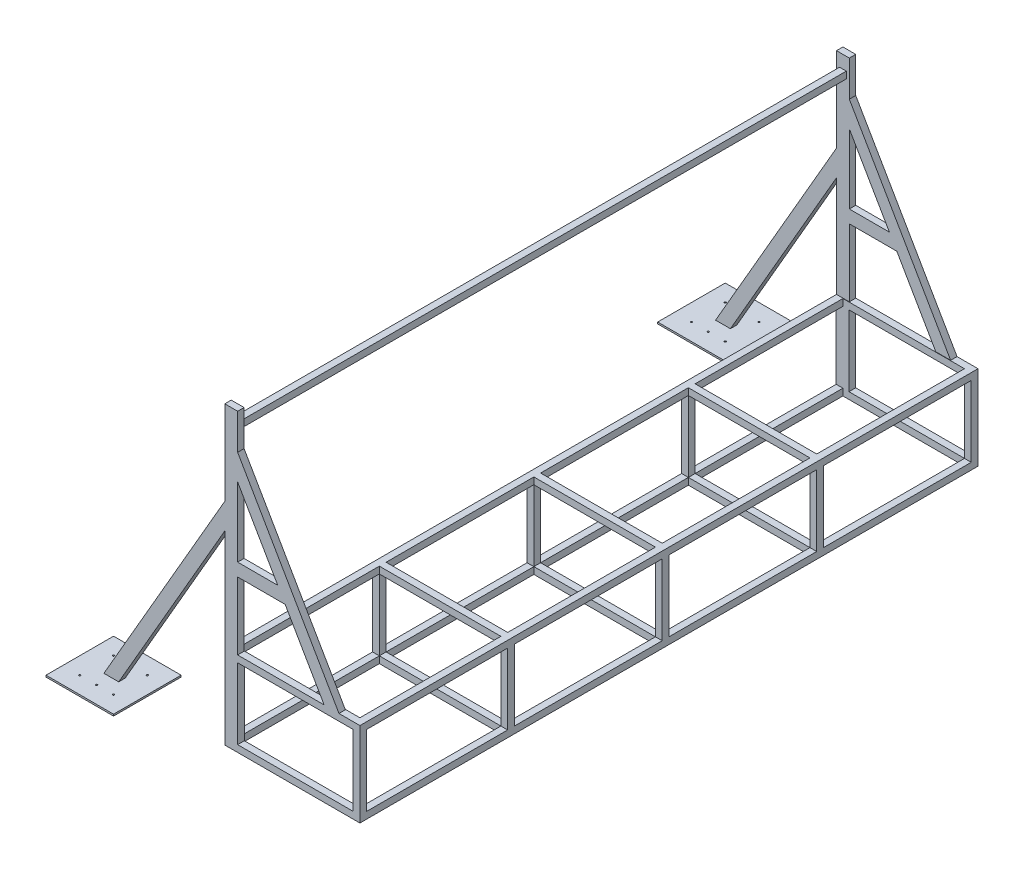
SolidWorks part; units mm, degrees
ref_plane "Front Plane" through (0, 0, 0) normal (0, 0, 1) x (1, 0, 0)
ref_plane "Top Plane" through (0, 0, 0) normal (0, 1, 0) x (1, 0, 0)
ref_plane "Right Plane" through (0, 0, 0) normal (1, 0, 0) x (0, 0, -1)
sketch "Sketch1" plane through (0, 0, 0) normal (0, 0, 1) x (1, 0, 0)
  line L0 (0, 0) -> (800, 0)
  line L1 (55, 0) -> (-55, 0) construction
  line L4 (800, 500) -> (800, 1426.2248) construction
  line L6 (0, 0) -> (0, 500)
  line L7 (0, 500) -> (800, 500)
  line L8 (800, 500) -> (800, 0)
  line L9 (0, 500) -> (0, 2000)
  line L10 (800, 500) -> (2630, 3669.653)
  line L11 (1715, 2084.8265) -> (0, 2000) construction
  line L12 (800, 0) -> (5182.5126, 0) construction
  line L13 (2805.4283, 4100) -> (3005.4283, 4100)
  line L14 (5.4283, 4100) -> (205.4283, 4100)
  line L15 (5.4283, 4100) -> (5.4283, 3700)
  line L16 (5.4283, 3700) -> (205.4283, 3700)
  line L17 (205.4283, 4100) -> (205.4283, 3700)
  line L18 (5.4283, 4100) -> (205.4283, 3700) construction
  line L19 (5.4283, 3700) -> (205.4283, 4100) construction
  line L20 (2805.4283, 4100) -> (2805.4283, 3700)
  line L21 (2805.4283, 3700) -> (3005.4283, 3700)
  line L22 (3005.4283, 4100) -> (3005.4283, 3700)
  line L23 (2805.4283, 4100) -> (3005.4283, 3700) construction
  line L24 (2805.4283, 3700) -> (3005.4283, 4100) construction
  line L25 (800, 500) -> (784.4115, 509)
  line L26 (1715, 2084.8265) -> (1160.2235, 2405.1269) construction
  line L27 (2630, 3669.653) -> (2630, 2940.232) construction
  line L28 (2630, 3669.653) -> (3156.2133, 3365.8436) construction
  line L29 (784.4115, 509) -> (2614.4115, 3678.653)
  line L30 (2614.4115, 3678.653) -> (2630, 3669.653)
  line L31 (5605.4283, 4100) -> (5805.4283, 4100)
  line L32 (5605.4283, 4100) -> (5605.4283, 3700)
  line L33 (5605.4283, 3700) -> (5805.4283, 3700)
  line L34 (5805.4283, 4100) -> (5805.4283, 3700)
  line L35 (5605.4283, 4100) -> (5805.4283, 3700) construction
  line L36 (5605.4283, 3700) -> (5805.4283, 4100) construction
  point P5 (105.4283, 3900)
  point P17 (2905.4283, 3900)
  point P22 (5705.4283, 3900)
  dimension "D1" = 800
  dimension "D2" = 500
  dimension "D3" = 1500
  dimension "D4" = 3660
  dimension "D5" = 30
  dimension "D6" = 3669.653
  dimension "D7" = 2630
  dimension "D8" = 1717.0965
  dimension "D9" = 200
  dimension "D10" = 400
  dimension "D11" = 3700
  dimension "D12" = 200
  dimension "D13" = 400
  dimension "D17" = 90
  dimension "D18" = 32.832
  dimension "D19" = 90
  dimension "D14" = 2600
  dimension "D15" = 18
  dimension "D16" = 200
  dimension "D20" = 400
  dimension "D21" = 2600
extrude "Boss-Extrude5" add sketch "Sketch1" along normal blind 3660 contours L8 L7 L6 L0 | L30 L29 L25 L10
ref_plane "Plane1" through (0, 0, 1830) normal (0, 0, 1) x (1, 0, 0)
sketch "Sketch3" plane through (0, 0, 0) normal (0, 0, 1) x (1, 0, 0)
  line L0 (0, 0) -> (-1677.1081, 0) construction
  line L1 (0, 500) -> (76, 500)
  line L2 (0, 500) -> (0, 1098)
  line L3 (0, 1750) -> (76, 1750)
  line L4 (76, 500) -> (76, 900)
  line L5 (0, 1250) -> (-721.6878, 0)
  line L6 (0, 1098) -> (-633.9306, 0)
  line L7 (0, 1250) -> (0, 1750)
  line L8 (0, 500) -> (0, 2000) construction
  line L9 (-633.9306, 0) -> (-721.6878, 0)
  line L10 (76, 1539.2305) -> (676, 500)
  line L11 (0, 500) -> (800, 500) construction
  line L12 (76, 1387.2305) -> (313.424, 976)
  line L14 (676, 500) -> (588.2428, 500)
  line L15 (76, 1539.2305) -> (76, 1750)
  line L16 (76, 976) -> (313.424, 976)
  line L17 (76, 900) -> (357.3027, 900)
  line L18 (76, 976) -> (76, 1387.2305)
  line L19 (357.3027, 900) -> (588.2428, 500)
  point P21 (376, 1019.6152)
  point P22 (-677.8092, 0)
  dimension "D3" = 76
  dimension "D4" = 1200
  dimension "D6" = 60
  dimension "D1" = 76
  dimension "D5" = 76
  dimension "D7" = 60
  dimension "D2" = 1750
  dimension "D8" = 76
  dimension "D9" = 400
extrude "Boss-Extrude2" add sketch "Sketch3" along normal blind 38
mirror "Mirror1" about plane through (0, 0, 1830) normal (0, 0, 1) of "Boss-Extrude2"
sketch "Sketch4" plane through (0, 0, 3660) normal (0, 0, 1) x (1, 0, 0)
  line L0 (800, 500) -> (800, 0) construction
  line L1 (76, 460) -> (760, 460)
  line L2 (76, 460) -> (76, 40)
  line L3 (76, 40) -> (760, 40)
  line L4 (760, 460) -> (760, 40)
  line L5 (0, 0) -> (800, 0) construction
  line L7 (0, 500) -> (800, 500) construction
  line L8 (0, 0) -> (0, 1098) construction
  dimension "D3" = 76
  dimension "D1" = 40
  dimension "D2" = 40
  dimension "D4" = 40
extrude "Cut-Extrude1" cut sketch "Sketch4" against normal through all
sketch "Sketch5" plane through (0, 0, 1830) normal (0, 0, 1) x (1, 0, 0)
  line L0 (40, 500) -> (40, 460)
  line L1 (40, 460) -> (0, 460)
  line L2 (0, 460) -> (0, 40)
  line L3 (0, 40) -> (40, 40)
  line L4 (40, 40) -> (40, 0)
  line L5 (40, 0) -> (760, 0)
  line L6 (760, 0) -> (760, 40)
  line L7 (760, 40) -> (800, 40)
  line L8 (800, 40) -> (800, 460)
  line L9 (800, 460) -> (760, 460)
  line L10 (760, 460) -> (760, 500)
  line L11 (760, 500) -> (40, 500)
  line L12 (800, 500) -> (800, 0) construction
  line L13 (0, 500) -> (800, 500) construction
  line L14 (0, 0) -> (0, 500) construction
  line L15 (0, 0) -> (800, 0) construction
  line L17 (0, 0) -> (0, 1098) construction
  dimension "D1" = 40
extrude "Cut-Extrude2" cut sketch "Sketch5" against normal offset from surface 40 and the other way offset from surface (1790 mm away) 40 up to face at (418, 250, 0)
sketch "Sketch7" plane through (367.9052, -212.4102, 0) normal (-0.866, 0.5, 0) x (0, 0, 1)
  line L0 (1830, 833.0127) -> (0, 833.0127)
  line L2 (0, 833.0127) -> (0, 4493.0127)
  line L3 (0, 4493.0127) -> (1830, 4493.0127)
  line L5 (1830, 4493.0127) -> (1830, 4455.0127)
  line L6 (1830, -275) -> (1830, 275) construction
  line L7 (1830, 4455.0127) -> (38, 4455.0127)
  line L8 (38, 4455.0127) -> (38, 871.0127)
  line L9 (38, 871.0127) -> (1830, 871.0127)
  line L10 (1830, 871.0127) -> (1830, 833.0127)
  dimension "D1" = 38
  dimension "D2" = 38
  dimension "D3" = 38
extrude "Boss-Extrude3" add sketch "Sketch7" along normal blind 76
mirror "Mirror2" about plane through (0, 0, 1830) normal (0, 0, 1) of "Boss-Extrude3"
sketch "Sketch8" plane through (367.9052, -212.4102, 0) normal (-0.866, 0.5, 0) x (0, 0, 1)
  line L1 (0, 833.0127) -> (2440, 833.0127)
  line L2 (0, 833.0127) -> (0, 2053.0127)
  line L3 (0, 2053.0127) -> (2440, 2053.0127)
  line L4 (2440, 833.0127) -> (2440, 2053.0127)
  line L5 (2440, 833.0127) -> (3660, 833.0127)
  line L6 (2440, 833.0127) -> (2440, 3273.0127)
  line L7 (2440, 3273.0127) -> (3660, 3273.0127)
  line L8 (3660, 833.0127) -> (3660, 3273.0127)
  line L9 (0, 833.0127) -> (0, 4493.0127) construction
  line L10 (2440, 3273.0127) -> (3660, 3273.0127)
  line L11 (2440, 3273.0127) -> (2440, 4493.0127)
  line L12 (2440, 4493.0127) -> (3660, 4493.0127)
  line L13 (3660, 3273.0127) -> (3660, 4493.0127)
  line L14 (2440, 3273.0127) -> (0, 3273.0127)
  line L15 (2440, 3273.0127) -> (2440, 2053.0127)
  line L16 (2440, 2053.0127) -> (0, 2053.0127)
  line L17 (0, 3273.0127) -> (0, 2053.0127)
  line L18 (2440, 3273.0127) -> (0, 3273.0127)
  line L19 (2440, 3273.0127) -> (2440, 4493.0127)
  line L20 (2440, 4493.0127) -> (0, 4493.0127)
  line L21 (0, 3273.0127) -> (0, 4493.0127)
  dimension "D1" = 1220
  dimension "D2" = 2440
  dimension "D3" = 2440
  dimension "D4" = 1220
  dimension "D5" = 1220
sketch "Sketch9" plane through (0, 0, 0) normal (0, -1, 0) x (1, 0, 0)
  line L0 (-721.6878, 3660) -> (-633.9306, 3660) construction
  line L1 (-477.8092, 3841) -> (-877.8092, 3841)
  line L2 (-477.8092, 3841) -> (-477.8092, 3441)
  line L3 (-477.8092, 3441) -> (-877.8092, 3441)
  line L4 (-877.8092, 3841) -> (-877.8092, 3441)
  line L5 (-477.8092, 3841) -> (-877.8092, 3441) construction
  line L6 (-477.8092, 3441) -> (-877.8092, 3841) construction
  line L7 (-677.8092, 3622) -> (-677.8092, 3660) construction
  line L8 (-721.6878, 3622) -> (-633.9306, 3622) construction
  line L9 (275, 1830) -> (-275, 1830) construction
  line L10 (-477.8092, -181) -> (-477.8092, 219)
  line L11 (-477.8092, 219) -> (-877.8092, 219)
  line L12 (-877.8092, -181) -> (-877.8092, 219)
  line L13 (-477.8092, -181) -> (-877.8092, -181)
  point P0 (-677.8092, 3641)
  point P11 (-677.8092, 3641)
  dimension "D1" = 400
  dimension "D2" = 400
extrude "Boss-Extrude6" add sketch "Sketch9" against normal blind 10
sketch "Sketch10" plane through (0, 0, 0) normal (0, 0, 1) x (1, 0, 0)
  line L1 (4364.3674, 1800) -> (4789.2316, 1800)
  line L2 (4364.3674, 1800) -> (4364.3674, 0)
  line L3 (4364.3674, 0) -> (4789.2316, 0)
  line L4 (4789.2316, 1800) -> (4789.2316, 0)
  line L5 (4364.3674, 1800) -> (4789.2316, 0) construction
  line L6 (4364.3674, 0) -> (4789.2316, 1800) construction
  point P0 (4576.7995, 900)
  dimension "D1" = 1800
sketch "Sketch11" plane through (0, 0, 38) normal (0, 0, 1) x (1, 0, 0)
  line L0 (76, 1750) -> (0, 1750) construction
  line L1 (58, 1634) -> (18, 1634)
  line L2 (58, 1634) -> (58, 1674)
  line L3 (58, 1674) -> (18, 1674)
  line L4 (18, 1634) -> (18, 1674)
  line L5 (58, 1634) -> (18, 1674) construction
  line L6 (58, 1674) -> (18, 1634) construction
  line L7 (0, 1750) -> (0, 1250) construction
  point P0 (38, 1654)
  dimension "D1" = 40
  dimension "D2" = 76
  dimension "D3" = 18
extrude "Boss-Extrude7" add sketch "Sketch11" along normal up to surface (3584 mm away) up to face at (155.1413, 1113.0768, 3622)
sketch "Sketch12" plane through (0, 40, 0) normal (0, 1, 0) x (1, 0, 0)
  line L1 (0, 0) -> (40, 0)
  line L2 (0, 0) -> (0, -40)
  line L3 (0, -40) -> (40, -40)
  line L4 (40, 0) -> (40, -40)
  line L5 (0, 0) -> (40, -40) construction
  line L6 (0, -40) -> (40, 0) construction
  line L7 (40, -40) -> (40, -3620) construction
  line L8 (0, -40) -> (0, -3620) construction
  line L9 (0, 0) -> (800, 0) construction
  point P0 (20, -20)
extrude "Boss-Extrude8" add sketch "Sketch12" along normal up to surface (420 mm away) up to face at (20, 460, 1830)
pattern_linear "LPattern1" count 4 spacing 915 along (0, 0, 1) count 2 spacing 760 along (1, 0, 0) of "Boss-Extrude8"
sketch "Sketch13" plane through (760, 0, 0) normal (-1, 0, 0) x (0, 0, 1)
  line L0 (0, 1250) -> (0, 0) construction
  line L1 (0, 500) -> (40, 500)
  line L2 (0, 500) -> (0, 460)
  line L3 (0, 460) -> (40, 460)
  line L4 (40, 500) -> (40, 460)
  line L5 (0, 500) -> (40, 460) construction
  line L6 (0, 460) -> (40, 500) construction
  line L7 (3660, 500) -> (0, 500) construction
  point P0 (20, 480)
  dimension "D1" = 40
extrude "Boss-Extrude9" add sketch "Sketch13" along normal up to surface (760 mm away) up to face at (0, 250, 3202.5)
pattern_linear "LPattern2" count 4 spacing 915 along (0, 0, 1) count 2 spacing 460 along (0, -1, 0) of "Boss-Extrude9"
sketch "Sketch14" plane through (0, 0, 3660) normal (0, 0, 1) x (1, 0, 0)
  line L0 (676, 500) -> (800, 500) construction
  line L1 (617.1788, 500) -> (4758.0267, 500)
  line L2 (617.1788, 500) -> (617.1788, 4035.8495)
  line L3 (617.1788, 4035.8495) -> (4758.0267, 4035.8495)
  line L4 (4758.0267, 500) -> (4758.0267, 4035.8495)
extrude "Cut-Extrude3" cut sketch "Sketch14" against normal through all both and the other way through all
hole_wizard "Ø10.0mm Dowel Hole1" positions "3DSketch1" profile "Sketch17" hole size "Ø10.0" standard "ISO" end condition through all
sketch3d "3DSketch1"
  line L0 (-777.8092, 10, 3541) -> (-777.8092, 10, 3441) construction
  line L1 (-877.8092, 10, 3441) -> (-477.8092, 10, 3441) construction
  line L3 (-777.8092, 10, 3541) -> (-877.8092, 10, 3541) construction
  line L4 (-877.8092, 10, 3841) -> (-877.8092, 10, 3441) construction
  point P0 (-777.8092, 10, 3541)
  dimension "D1" = 100
sketch "Sketch17" plane through (-777.8092, 10, 3541) normal (1, 0, 0) x (0, 0, 1)
  line L0 (0, 0) -> (0, 10)
  line L1 (0, 10) -> (5, 10)
  line L2 (5, 10) -> (5, 0)
  line L5 (5, 0) -> (0, 0)
  line L11 (0, -6.35) -> (0, 107.95) construction
  dimension "Thru Hole Dia." = 10
  dimension "Thru Hole Depth" = 10
pattern_linear "LPattern3" count 2 spacing 200 along (0, 0, 1) count 3 spacing 100 along (1, 0, 0) of "Ø10.0mm Dowel Hole1"
mirror "Mirror3" about plane through (0, 0, 1830) normal (0, 0, 1) of "LPattern3", "Ø10.0mm Dowel Hole1"
equation "\"alpha\"= 30deg'\"Wall Angle\""
equation "\"D5@Sketch1\"=\"alpha\""
equation "\"Frame steel height\"= 76mm"
equation "\"Frame steel length\"= 38mm"
equation "\"Support square tube size\"= 40mm"
equation "\"D3@Sketch3\"=\"Frame steel height\""
equation "\"D1@Sketch4\"=\"Support square tube size\""
equation "\"D2@Sketch4\"=\"Support square tube size\""
equation "\"D4@Sketch4\"=\"Support square tube size\""
equation "\"Wall width\"= 3660mm"
equation "\"D1@Cut-Extrude2\"=\"Support square tube size\""
equation "\"D2@Cut-Extrude2\"=\"Support square tube size\""
equation "\"D1@Sketch7\"=\"Frame steel length\""
equation "\"D2@Sketch7\"=\"Frame steel length\""
equation "\"D3@Sketch7\"=\"Frame steel length\""
equation "\"D1@Boss-Extrude3\"=\"Frame steel height\""
equation "\"D1@Boss-Extrude5\"=\"Wall width\""
equation "\"D1@Boss-Extrude6\"=10mm"
equation "\"D1@Sketch3\"=\"Frame steel height\""
equation "\"D1@Sketch5\"=\"Support square tube size\""
equation "\"D3@Sketch4\"=\"Frame steel height\""
equation "\"D1@Sketch11\"=\"Support square tube size\""
equation "\"D2@Sketch11\"=\"Frame steel height\""
equation "\"D3@Sketch11\"=(\"Frame steel height\"-\"Support square tube size\")/2"
equation "\"D1@Boss-Extrude2\"=\"Frame steel length\""
equation "\"D5@Sketch3\"=\"Frame steel height\""
equation "\"D3@LPattern1\"=\"Wall width\"/4"
equation "\"D4@LPattern1\"=760"
equation "\"D1@Sketch13\"=\"Support square tube size\""
equation "\"D3@LPattern2\"=\"Wall width\"/4"
equation "\"D4@LPattern2\"=500-\"Support square tube size\""
equation "\"D8@Sketch3\"=\"Frame steel height\""
